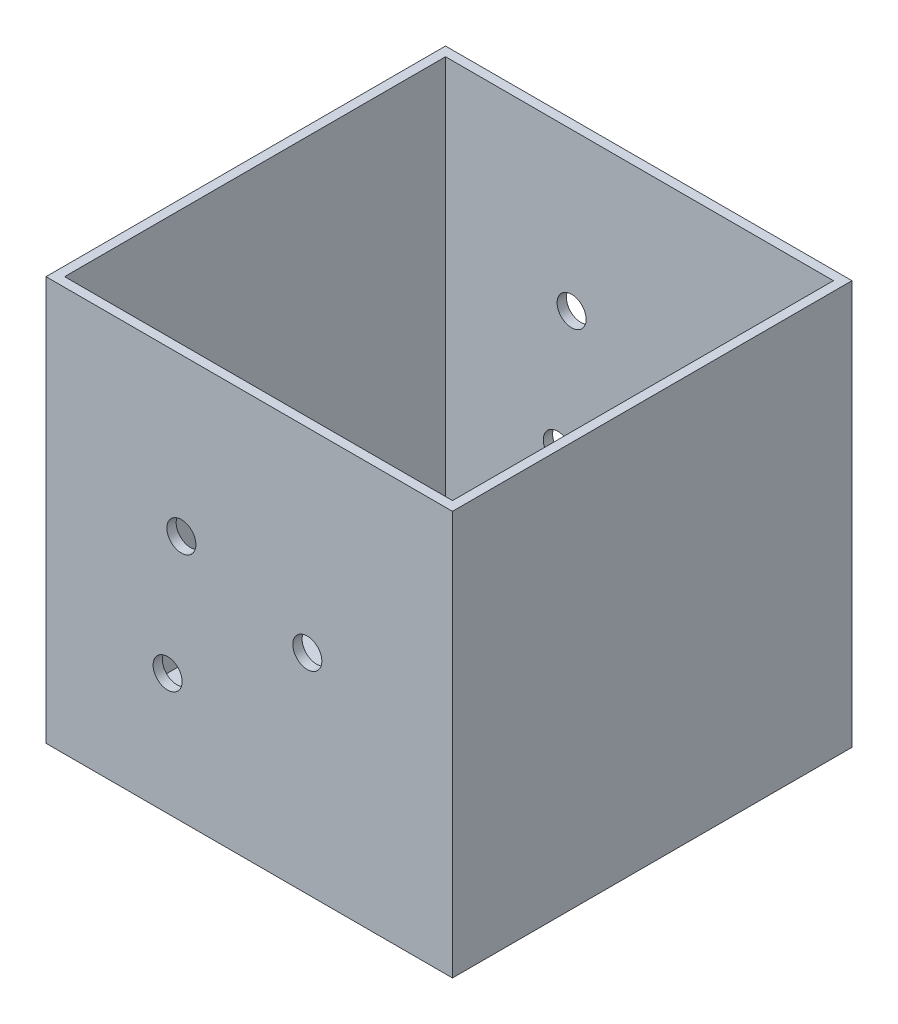
SolidWorks part; units mm, degrees
ref_plane "Ön Düzlem" through (0, 0, 0) normal (0, 0, 1) x (1, 0, 0)
ref_plane "Üst Düzlem" through (0, 0, 0) normal (0, 1, 0) x (1, 0, 0)
ref_plane "Sağ Düzlem" through (0, 0, 0) normal (1, 0, 0) x (0, 0, -1)
sketch "Çizim1" plane through (0, 0, 0) normal (0, 0, 1) x (1, 0, 0)
  line L1 (-225, 168) -> (125, 168)
  line L2 (-225, 168) -> (-225, -180)
  line L3 (-225, -180) -> (125, -180)
  line L4 (125, 168) -> (125, -180)
  line L5 (-213, 156) -> (113, 156) construction
  line L6 (-213, 156) -> (-213, -168) construction
  line L7 (-213, -168) -> (113, -168) construction
  line L8 (113, 156) -> (113, -168) construction
  circle A0 centre (0, 0) radius 16.5 construction
  circle A1 centre (-108.4405, 32.6529) radius 96.75 construction
  circle A2 centre (-108.4405, 32.6529) radius 21.25 construction
  circle A3 centre (-120.2975, -75.4488) radius 87.5 construction
  circle A4 centre (-120.2975, -75.4488) radius 34 construction
  circle A5 centre (0, 0) radius 108 construction
  circle A6 centre (0, 0) radius 125
  circle A7 centre (0, 0) radius 12.5
  circle A8 centre (-108.4405, 32.6529) radius 12.5
  circle A9 centre (-120.2975, -75.4488) radius 12.5
  dimension "D1" = 33
  dimension "D2" = 193.5
  dimension "D3" = 42.5
  dimension "D4" = 175
  dimension "D5" = 68
  dimension "D6" = 216
  dimension "D10" = 250
  dimension "D15" = 193.5
  dimension "D16" = 25
  dimension "D17" = 25
  dimension "D18" = 25
  dimension "D7" = 350
  dimension "D8" = 348
  dimension "D9" = 180
  dimension "D11" = 12
  dimension "D12" = 12
  dimension "D13" = 12
  dimension "D14" = 12
extrude "Yükseklik-Ekstrüzyon4" add sketch "Çizim1" against normal blind 344 contours A8 A6 L4 L1 L2 L3 A9 | A8 A6 A7
shell "İç Boşaltma2" thickness 8
